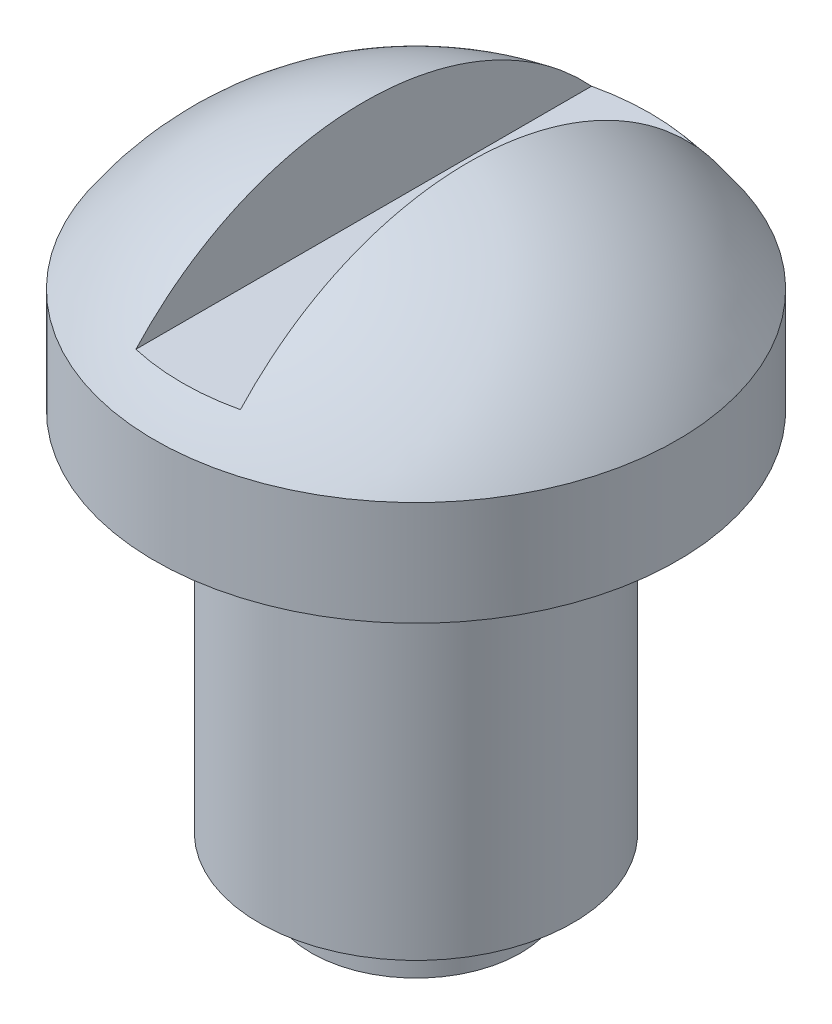
SolidWorks part; units mm, degrees
ref_plane "Front Plane" through (0, 0, 0) normal (0, 0, 1) x (1, 0, 0)
ref_plane "Top Plane" through (0, 0, 0) normal (0, 1, 0) x (1, 0, 0)
ref_plane "Right Plane" through (0, 0, 0) normal (1, 0, 0) x (0, 0, -1)
sketch "Sketch1" plane through (0, 0, 0) normal (0, 0, 1) x (1, 0, 0)
  line L0 (0, 12.6834) -> (0, 0)
  line L4 (5, 10) -> (5, 8)
  line L10 (3, 1) -> (3, 8)
  line L11 (0, 15.2489) -> (0, -10.6239) construction
  line L13 (0, 0) -> (2, 0)
  line L14 (2, 0) -> (2, 1)
  line L15 (3, 8) -> (5, 8)
  line L16 (2, 1) -> (3, 1)
  arc A0 (0, 12.6834) -> (5, 10) centre (0, 6.6834) cw
  point P0 (0, 15.2489)
  dimension "D3" = 1
  dimension "D4" = 2
  dimension "D5" = 6
  dimension "D1" = 7
  dimension "D2" = 2
  dimension "D6" = 3
  dimension "D7" = 5
revolve "Revolve1" add sketch "Sketch1" angle 360 about L11
sketch "Sketch2" plane through (0, 0, 0) normal (0, 0, 1) x (1, 0, 0)
  line L1 (-1, 13.6834) -> (1, 13.6834)
  line L2 (-1, 13.6834) -> (-1, 10.6834)
  line L3 (-1, 10.6834) -> (1, 10.6834)
  line L4 (1, 13.6834) -> (1, 10.6834)
  arc A0 (5, 10) -> (-5, 10) centre (0, 6.6834) ccw construction
  point P4 (0, 10.6834)
  point P5 (0, 12.6834)
  dimension "D1" = 2
  dimension "D2" = 2
  dimension "D3" = 3
extrude "Cut-Extrude1" cut sketch "Sketch2" against normal through all both and the other way through all
